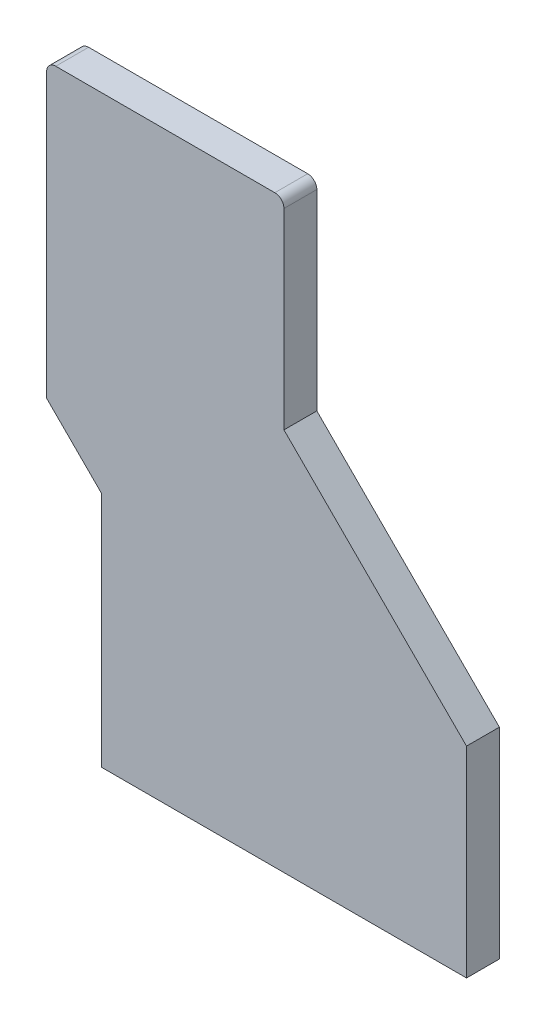
SolidWorks part; units mm, degrees
material "Balsa"
ref_plane "Front Plane" through (0, 0, 0) normal (0, 0, 1) x (1, 0, 0)
ref_plane "Top Plane" through (0, 0, 0) normal (0, 1, 0) x (1, 0, 0)
ref_plane "Right Plane" through (0, 0, 0) normal (1, 0, 0) x (0, 0, -1)
sketch "Sketch1" plane through (0, 0, 0) normal (0, 0, 1) x (1, 0, 0)
  line L0 (4.0702, 148.4877) -> (4.0702, 43.4877)
  line L1 (-95.9298, 153.4877) -> (-0.9298, 153.4877)
  line L2 (-95.9298, -36.5123) -> (-95.9298, -166.5123)
  line L3 (-95.9298, -166.5123) -> (104.0702, -166.5123)
  line L4 (104.0702, -56.5123) -> (104.0702, -166.5123)
  line L5 (-95.9298, 153.4877) -> (104.0702, -166.5123) construction
  line L6 (-95.9298, -166.5123) -> (96.4747, 167.458) construction
  line L7 (4.0702, 43.4877) -> (104.0702, -56.5123)
  line L8 (-95.9298, 153.4877) -> (-120.9298, 153.4877)
  line L9 (-125.9298, 148.4877) -> (-125.9298, -6.5123)
  line L10 (-125.9298, -6.5123) -> (-95.9298, -36.5123)
  arc A0 (-120.9298, 153.4877) -> (-125.9298, 148.4877) centre (-120.9298, 148.4877) ccw
  arc A1 (4.0702, 148.4877) -> (-0.9298, 153.4877) centre (-0.9298, 148.4877) ccw
  point P0 (0, 0)
  point P11 (-125.9298, 153.4877)
  point P17 (4.0702, 153.4877)
  dimension "D3" = 110
  dimension "D6" = 5
  dimension "D9" = 130
  dimension "D10" = 160
  dimension "D1" = 30
  dimension "D2" = 320
  dimension "D4" = 100
  dimension "D5" = 110
  dimension "D29" = 200
extrude "Boss-Extrude1" add sketch "Sketch1" along normal blind 18
